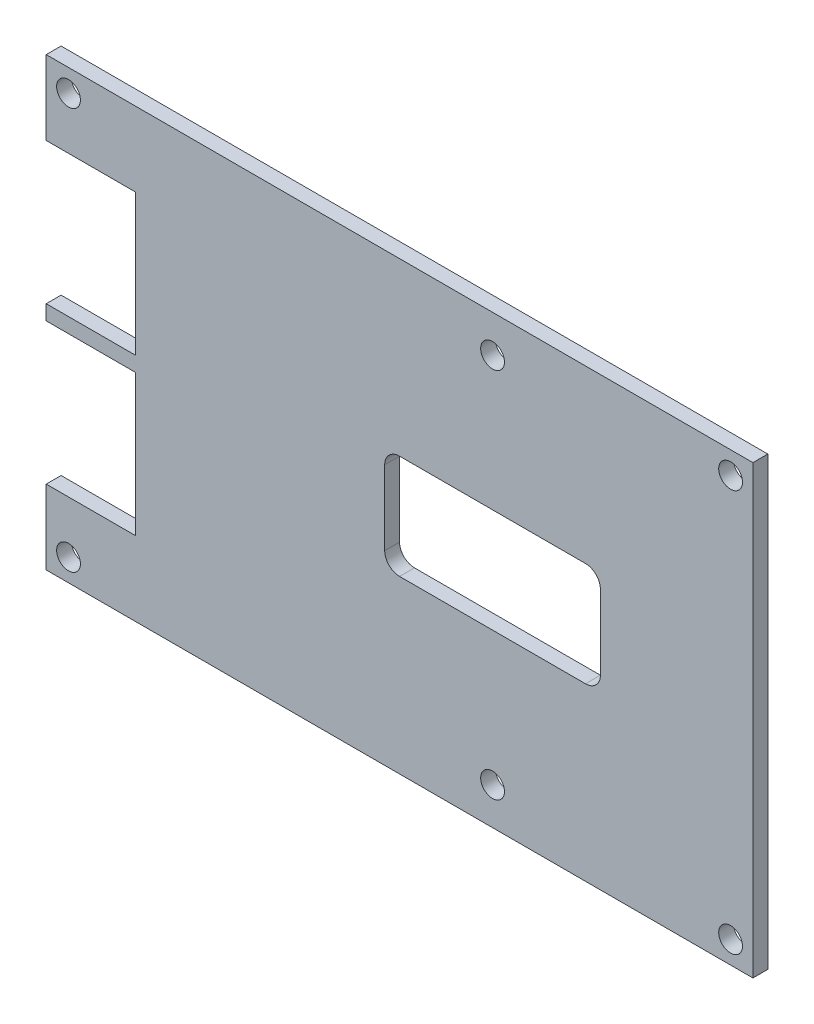
SolidWorks part; units mm, degrees
ref_plane "Front Plane" through (0, 0, 0) normal (0, 0, 1) x (1, 0, 0)
ref_plane "Top Plane" through (0, 0, 0) normal (0, 1, 0) x (1, 0, 0)
ref_plane "Right Plane" through (0, 0, 0) normal (1, 0, 0) x (0, 0, -1)
sketch "Sketch1" plane through (0, 0, 0) normal (0, 0, 1) x (1, 0, 0)
  line L0 (20.4364, -36.1185) -> (20.4364, -11.1185) construction
  line L1 (-39.5636, 18.8815) -> (55.4364, 18.8815)
  line L2 (-39.5636, 18.8815) -> (-39.5636, 8.8815)
  line L3 (-39.5636, -41.1185) -> (55.4364, -41.1185)
  line L4 (55.4364, 18.8815) -> (55.4364, -41.1185)
  line L5 (20.4364, -4.1185) -> (20.4364, -11.1185) construction
  line L6 (7.9364, -4.1185) -> (32.9364, -4.1185)
  line L7 (5.9364, -6.1185) -> (5.9364, -16.1185)
  line L8 (7.9364, -18.1185) -> (32.9364, -18.1185)
  line L9 (34.9364, -6.1185) -> (34.9364, -16.1185)
  line L10 (20.4364, -18.1185) -> (20.4364, -11.1185) construction
  line L11 (20.4364, -11.1185) -> (20.4364, 13.8815) construction
  line L12 (-39.5636, -10.1185) -> (-39.5636, -12.1185)
  line L13 (-39.5636, 8.8815) -> (-27.5636, 8.8815)
  line L15 (-39.5636, -10.1185) -> (-27.5636, -10.1185)
  line L16 (-27.5636, 8.8815) -> (-27.5636, -10.1185)
  line L17 (-39.5636, -31.1185) -> (-39.5636, -41.1185)
  line L18 (-39.5636, -12.1185) -> (-27.5636, -12.1185)
  line L20 (-39.5636, -31.1185) -> (-27.5636, -31.1185)
  line L21 (-27.5636, -12.1185) -> (-27.5636, -31.1185)
  line L22 (-27.5636, 8.8815) -> (-27.5636, 18.8815) construction
  line L23 (-27.5636, -31.1185) -> (-27.5636, -41.1185) construction
  circle A0 centre (20.4364, 13.8815) radius 1.6
  circle A1 centre (20.4364, -36.1185) radius 1.6
  circle A2 centre (-36.5636, 15.8815) radius 1.6
  circle A3 centre (52.4364, 15.8815) radius 1.6
  circle A4 centre (-36.5636, -38.1185) radius 1.6
  circle A5 centre (52.4364, -38.1185) radius 1.6
  arc A6 (7.9364, -4.1185) -> (5.9364, -6.1185) centre (7.9364, -6.1185) ccw
  arc A7 (34.9364, -6.1185) -> (32.9364, -4.1185) centre (32.9364, -6.1185) ccw
  arc A8 (7.9364, -18.1185) -> (5.9364, -16.1185) centre (7.9364, -16.1185) cw
  arc A9 (32.9364, -18.1185) -> (34.9364, -16.1185) centre (32.9364, -16.1185) ccw
  point P36 (0, 0)
  point P41 (0, 0)
  point P43 (47.1574, -11.1185)
  point P44 (20.4364, 11.6787)
  point P45 (20.4364, -31.1185)
  dimension "D3" = 50
  dimension "D6" = 2
  dimension "D7" = 2
  dimension "D8" = 2
  dimension "D9" = 2
  dimension "D1" = 60
  dimension "D2" = 95
  dimension "D10" = 25
  dimension "D11" = 10
  dimension "D12" = 3
  dimension "D13" = 3
  dimension "D14" = 3
  dimension "D15" = 3
  dimension "D16" = 3
  dimension "D17" = 3
  dimension "D18" = 3
  dimension "D19" = 3
  dimension "D20" = 54
  dimension "D21" = 12
  dimension "D22" = 19
  dimension "D23" = 10
extrude "Boss-Extrude1" add sketch "Sketch1" along normal blind 2
